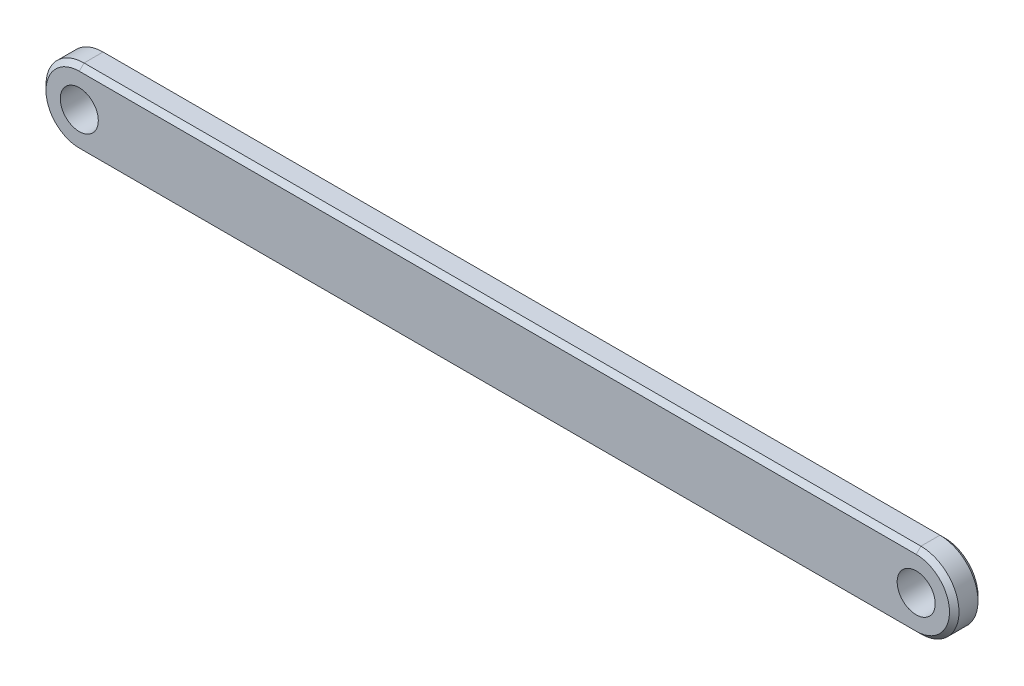
SolidWorks part; units mm, degrees
ref_plane "Front Plane" through (0, 0, 0) normal (0, 0, 1) x (1, 0, 0)
ref_plane "Top Plane" through (0, 0, 0) normal (0, 1, 0) x (1, 0, 0)
ref_plane "Right Plane" through (0, 0, 0) normal (1, 0, 0) x (0, 0, -1)
sketch "Sketch1" plane through (0, 0, 0) normal (0, 0, 1) x (1, 0, 0)
  line L0 (-44, 0) -> (44, 0) construction
  line L1 (-44, 4) -> (44, 4)
  line L2 (-44, -4) -> (44, -4)
  arc A0 (-44, 4) -> (-44, -4) centre (-44, 0) ccw
  arc A1 (44, -4) -> (44, 4) centre (44, 0) ccw
  circle A2 centre (-44, 0) radius 2
  circle A3 centre (44, 0) radius 2
  point P3 (0, 0)
  dimension "D2" = 8
  dimension "D3" = 4
  dimension "D4" = 4
  dimension "D5" = 4
  dimension "D1" = 88
extrude "Boss-Extrude1" add sketch "Sketch1" along normal blind 3
chamfer "Chamfer1" distance 0.5 angle 45 8 edges at (-48, 0, 0) (0, -4, 0) (48, 0, 0) (0, 4, 0) (-48, 0, 3) (0, 4, 3) (48, 0, 3) (0, -4, 3)
